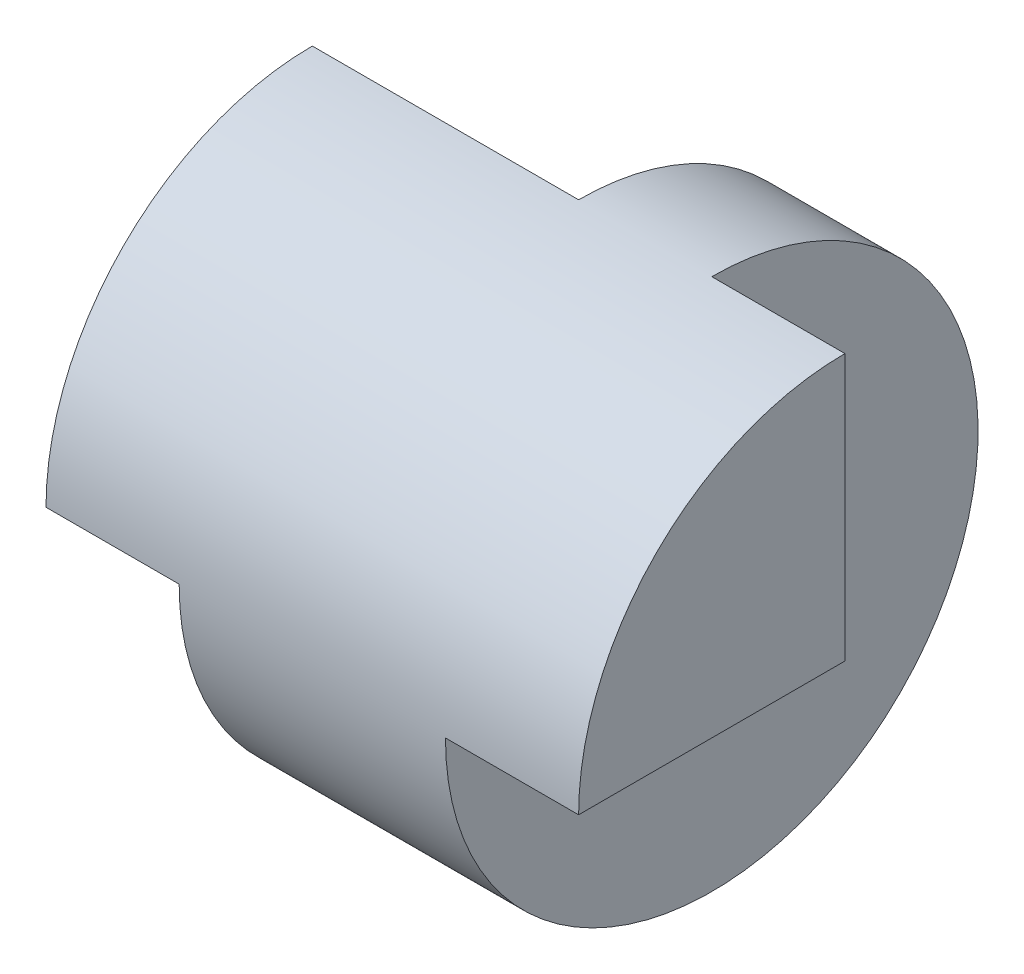
SolidWorks part; units mm, degrees
ref_plane "Front Plane" through (0, 0, 0) normal (0, 0, 1) x (1, 0, 0)
ref_plane "Top Plane" through (0, 0, 0) normal (0, 1, 0) x (1, 0, 0)
ref_plane "Right Plane" through (0, 0, 0) normal (1, 0, 0) x (0, 0, -1)
sketch "Sketch5" plane through (0, 0, 0) normal (0, 0, 1) x (1, 0, 0)
  line L0 (0, 0) -> (4, 0)
  dimension "D1" = 4
revolve "Revolve-Thin2" add sketch "Sketch5" angle 360 about L0 wall 2
sketch "Sketch6" plane through (0, 0, 0) normal (0, 0, 1) x (1, 0, 0)
  line L1 (1, 0) -> (0, 0)
  line L2 (1, 0) -> (1, -2)
  line L3 (1, -2) -> (0, -2)
  line L4 (0, 0) -> (0, -2)
  line L5 (4, -2) -> (3, -2)
  line L6 (4, -2) -> (4, 0)
  line L7 (4, 0) -> (3, 0)
  line L8 (3, -2) -> (3, 0)
  dimension "D1" = 1
  dimension "D2" = 1
  dimension "D3" = 2
  dimension "D4" = 2
extrude "Cut-Extrude5" cut sketch "Sketch6" against normal mid plane 11 contours L5 L8 L7 L6 | L4 L1 L2 L3 | L1 L4 L3 L2 | L8 L5 L6 L7
sketch "Sketch7" plane through (0, 0, 0) normal (0, -1, 0) x (1, 0, 0)
  line L1 (0, -2) -> (2, -2)
  line L2 (0, -2) -> (0, 0)
  line L3 (0, 0) -> (2, 0)
  line L4 (2, -2) -> (2, 0)
  line L5 (4, -2) -> (3, -2)
  line L6 (4, -2) -> (4, 0)
  line L7 (4, 0) -> (3, 0)
  line L8 (3, -2) -> (3, 0)
  dimension "D1" = 2
  dimension "D2" = 2
  dimension "D3" = 2
  dimension "D4" = 1
extrude "Cut-Extrude6" cut sketch "Sketch7" against normal blind 10
